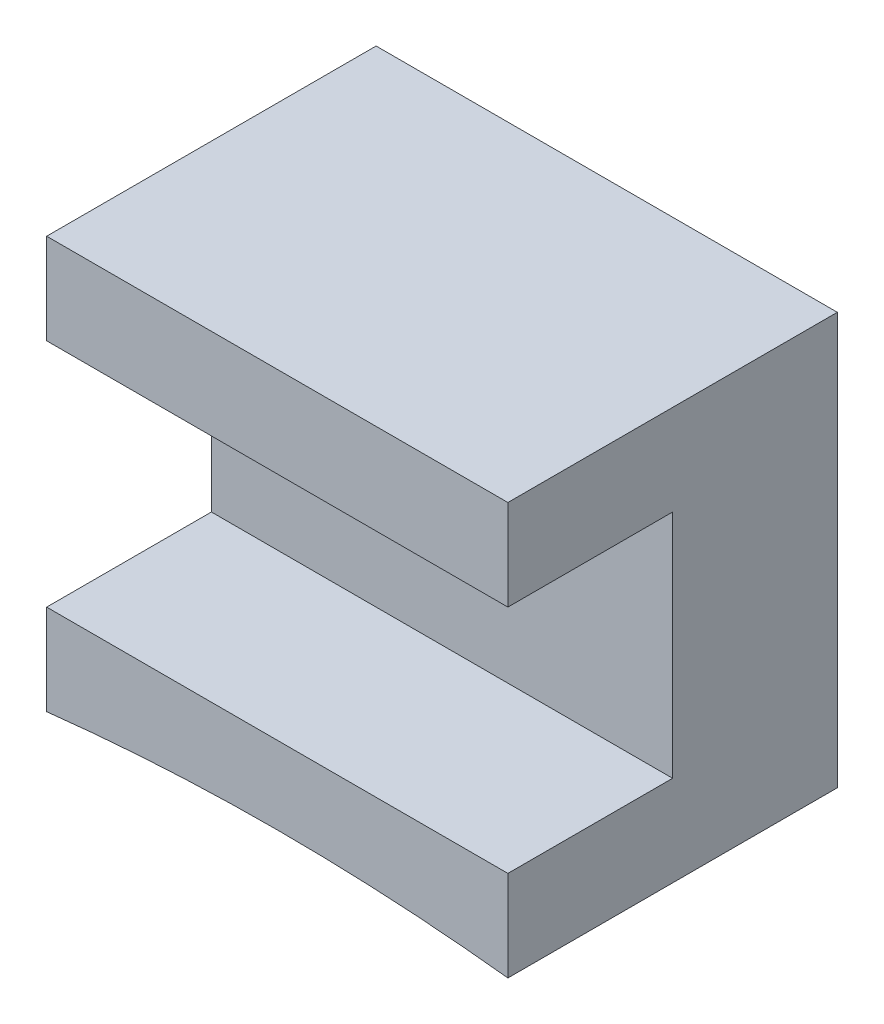
SolidWorks part; units mm, degrees
ref_plane "Front Plane" through (0, 0, 0) normal (0, 0, 1) x (1, 0, 0)
ref_plane "Top Plane" through (0, 0, 0) normal (0, 1, 0) x (1, 0, 0)
ref_plane "Right Plane" through (0, 0, 0) normal (1, 0, 0) x (0, 0, -1)
sketch "Sketch1" plane through (0, 0, 0) normal (0, 0, 1) x (1, 0, 0)
  line L1 (-3.556, -0.1998) -> (-3.556, 6.1502)
  line L2 (3.556, -0.1998) -> (3.556, 6.1502)
  line L3 (-3.556, 6.1502) -> (3.556, 6.1502)
  arc A0 (-3.556, -0.1998) -> (3.556, -0.1998) centre (0, -31.75) cw
  point P3 (0, 0)
  dimension "D1" = 31.75
  dimension "D2" = 0
  dimension "D3" = 0
  dimension "D4" = 7.112
  dimension "D5" = 6.35
  dimension "D6" = 6.35
extrude "Boss-Extrude1" add sketch "Sketch1" along normal blind 5.08
sketch "Sketch2" plane through (0, 0, 5.08) normal (0, 0, 1) x (1, 0, 0)
  line L0 (-3.556, 6.1502) -> (-3.556, -0.1998) construction
  line L1 (-3.556, 4.7532) -> (3.556, 4.7532)
  line L2 (-3.556, 4.7532) -> (-3.556, 1.1972)
  line L3 (-3.556, 1.1972) -> (3.556, 1.1972)
  line L4 (3.556, 4.7532) -> (3.556, 1.1972)
  line L5 (3.556, -0.1998) -> (3.556, 6.1502) construction
  dimension "D1" = 1.397
  dimension "D2" = 3.556
extrude "Cut-Extrude1" cut sketch "Sketch2" against normal blind 2.54
